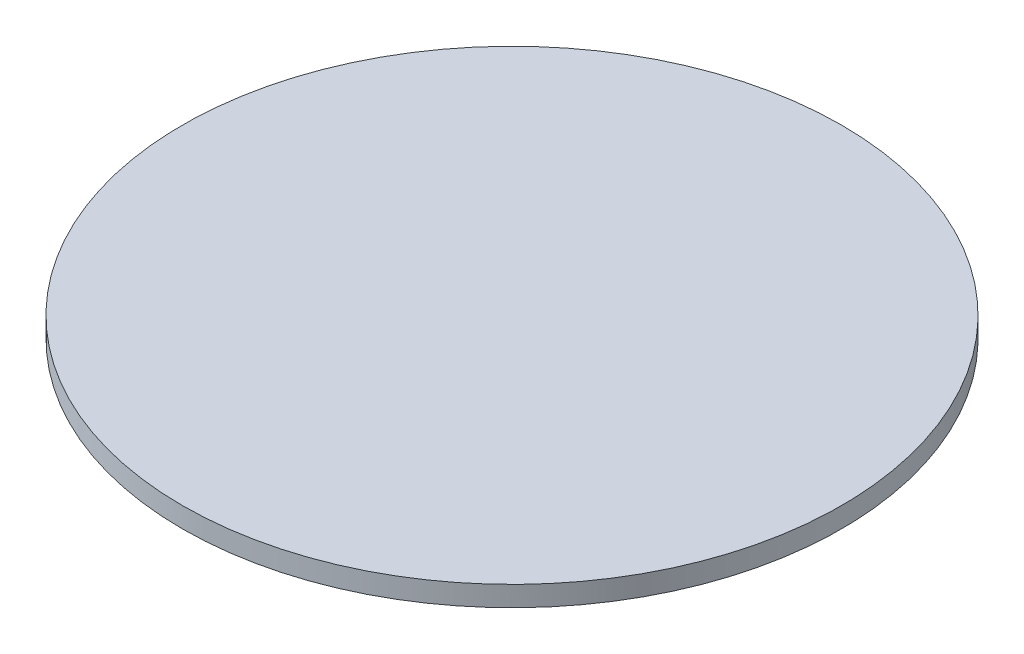
SolidWorks part; units mm, degrees
ref_plane "Front Plane" through (0, 0, 0) normal (0, 0, 1) x (1, 0, 0)
ref_plane "Top Plane" through (0, 0, 0) normal (0, 1, 0) x (1, 0, 0)
ref_plane "Right Plane" through (0, 0, 0) normal (1, 0, 0) x (0, 0, -1)
sketch "Sketch1" plane through (0, 0, 0) normal (0, 1, 0) x (1, 0, 0)
  circle A0 centre (0, 0) radius 16.3
  dimension "D1" = 32.6
extrude "Boss-Extrude1" add sketch "Sketch1" along normal blind 1
